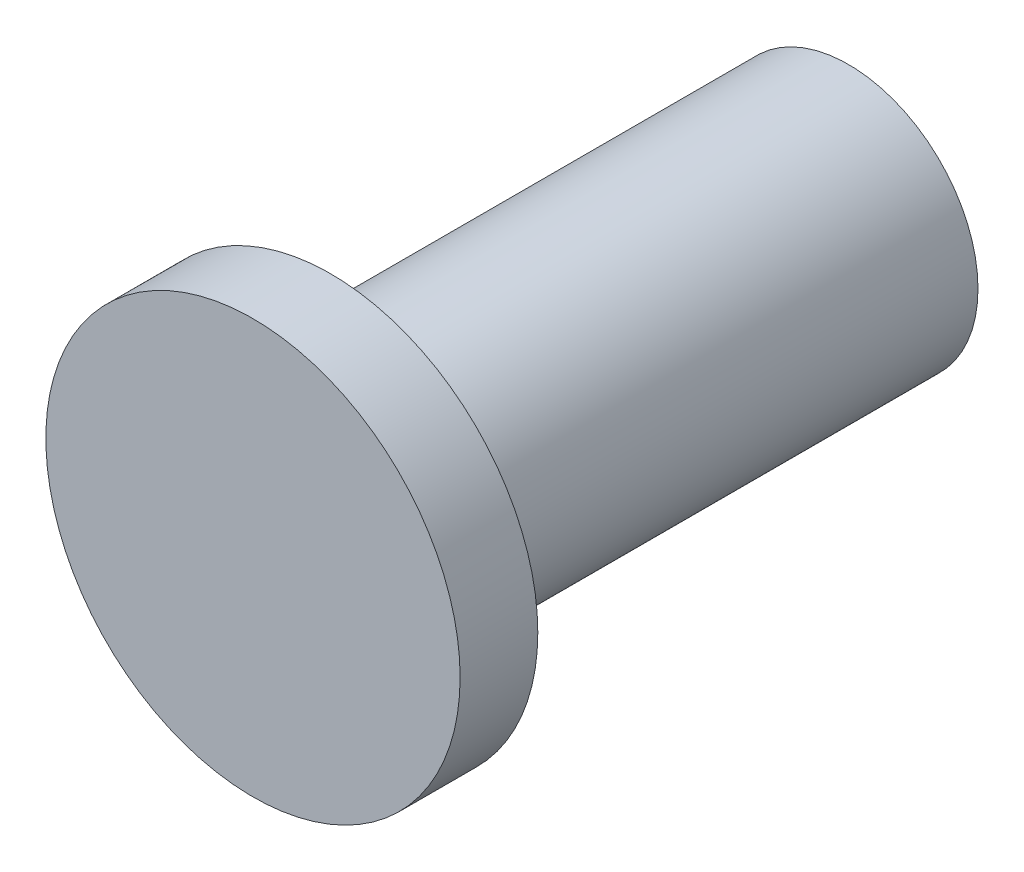
SolidWorks part; units mm, degrees
ref_plane "Front Plane" through (0, 0, 0) normal (0, 0, 1) x (1, 0, 0)
ref_plane "Top Plane" through (0, 0, 0) normal (0, 1, 0) x (1, 0, 0)
ref_plane "Right Plane" through (0, 0, 0) normal (1, 0, 0) x (0, 0, -1)
sketch "Sketch1" plane through (0, 0, 0) normal (0, 0, 1) x (1, 0, 0)
  circle A0 centre (0, 0) radius 8
  dimension "D1" = 16
extrude "Boss-Extrude1" add sketch "Sketch1" along normal blind 3
sketch "Sketch2" plane through (0, 0, 0) normal (0, 0, -1) x (-1, 0, 0)
  circle A0 centre (0, 0) radius 5
extrude "Boss-Extrude2" add sketch "Sketch2" along normal blind 10
sketch "Sketch3" plane through (0, 0, -10) normal (0, 0, -1) x (-1, 0, 0)
  circle A0 centre (0, 0) radius 5
extrude "Boss-Extrude3" add sketch "Sketch3" along normal blind 10
